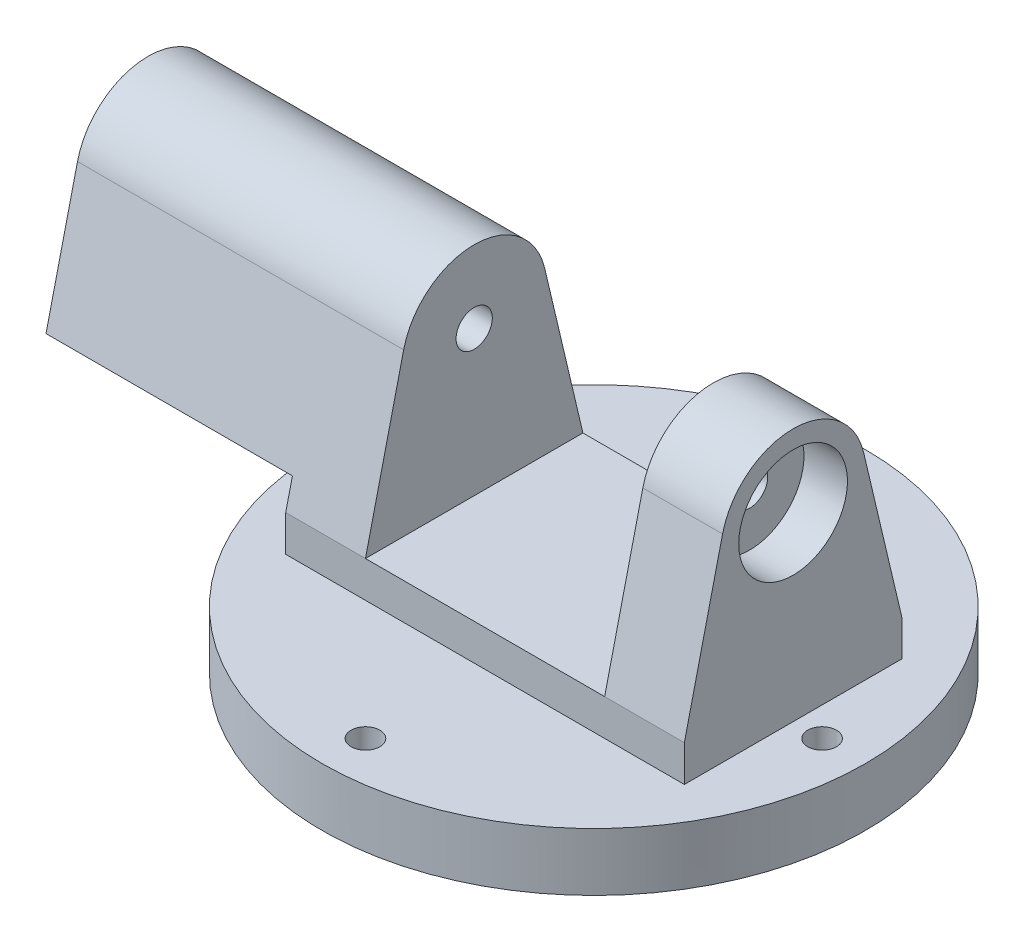
SolidWorks part; units mm, degrees
ref_plane "Alzado" through (0, 0, 0) normal (0, 0, 1) x (1, 0, 0)
ref_plane "Planta" through (0, 0, 0) normal (0, 1, 0) x (1, 0, 0)
ref_plane "Vista lateral" through (0, 0, 0) normal (1, 0, 0) x (0, 0, -1)
sketch "Croquis1" plane through (0, 0, 0) normal (0, 1, 0) x (1, 0, 0)
  circle A0 centre (0, 0) radius 75
extrude "Saliente-Extruir1" add sketch "Croquis1" along normal blind 8
sketch "Croquis2" plane through (0, 8, 0) normal (0, 1, 0) x (1, 0, 0)
  line L0 (0, 75) -> (0, 63) construction
  circle A0 centre (0, 0) radius 75 construction
  circle A1 centre (0, 63) radius 3.97
  circle A2 centre (63, 0) radius 3.97
  circle A3 centre (0, -63) radius 3.97
  circle A4 centre (-63, 0) radius 3.97
  point P15 (0, 0)
  dimension "D1" = 4
extrude "Cortar-Extruir1" cut sketch "Croquis2" against normal blind 20
sketch "Croquis3" plane through (0, 8, 0) normal (0, 1, 0) x (1, 0, 0)
  line L0 (-75, 0) -> (-55, 0) construction
  line L1 (75, 0) -> (55, 0) construction
  line L2 (-55, 0) -> (-55, 30)
  line L3 (-55, 30) -> (55, 30)
  line L4 (55, 30) -> (55, 0)
  line L5 (55, 0) -> (55, -30)
  line L6 (55, -30) -> (-55, -30)
  line L7 (-55, -30) -> (-55, 0)
  circle A0 centre (0, 0) radius 75 construction
extrude "Saliente-Extruir2" add sketch "Croquis3" along normal blind 10
sketch "Croquis4" plane through (55, 0, 0) normal (1, 0, 0) x (0, 0, -1)
  line L0 (-30, 18) -> (30, 18)
  line L2 (-30, 18) -> (-19.4643, 62.5982)
  line L3 (30, 18) -> (19.4643, 62.5982)
  arc A0 (19.4643, 62.5982) -> (-19.4643, 62.5982) centre (0, 58) ccw
extrude "Saliente-Extruir3" add sketch "Croquis4" against normal blind 22
mirror "Simetría1" about plane through (0, 0, 0) normal (1, 0, 0) of "Saliente-Extruir3"
sketch "Croquis5" plane through (-55, 0, 0) normal (-1, 0, 0) x (0, 0, 1)
  line L0 (0, 78) -> (0, 58) construction
  arc A0 (19.4643, 62.5982) -> (-19.4643, 62.5982) centre (0, 58) ccw construction
  circle A1 centre (0, 58) radius 15
extrude "Cortar-Extruir2" cut sketch "Croquis5" against normal blind 12
mirror "Simetría2" about plane through (0, 0, 0) normal (1, 0, 0) of "Cortar-Extruir2"
sketch "Croquis6" plane through (-43, 0, 0) normal (-1, 0, 0) x (0, 0, 1)
  line L0 (0, 73) -> (0, 58) construction
  circle A0 centre (0, 58) radius 15 construction
  circle A1 centre (0, 58) radius 5
extrude "Cortar-Extruir3" cut sketch "Croquis6" against normal blind 126
sketch "Croquis7" plane through (-55, 0, 0) normal (-1, 0, 0) x (0, 0, 1)
  line L0 (-19.4643, 62.5982) -> (-28.1515, 25.8247)
  line L1 (-30, 18) -> (-19.4643, 62.5982) construction
  line L2 (-28.1515, 25.8247) -> (28.1515, 25.8247)
  line L3 (19.4643, 62.5982) -> (30, 18) construction
  line L4 (28.1515, 25.8247) -> (19.4643, 62.5982)
  arc A0 (19.4643, 62.5982) -> (-19.4643, 62.5982) centre (0, 58) ccw
  circle A1 centre (0, 58) radius 15
extrude "Saliente-Extruir4" add sketch "Croquis7" along normal blind 68
sketch "Croquis8" plane through (0, 0, 0) normal (0, -1, 0) x (1, 0, 0)
  circle A2 centre (0, 0) radius 75
  circle A3 centre (0, 0) radius 75
  dimension "D1" = 0
extrude "Saliente-Extruir5" add sketch "Croquis8" along normal blind 8
sketch "Croquis9" plane through (0, -8, 0) normal (0, -1, 0) x (1, 0, 0)
  circle A0 centre (0, 0) radius 13
  circle A1 centre (0, 0) radius 15
  dimension "D1" = 26
  dimension "D2" = 30
extrude "Saliente-Extruir6" add sketch "Croquis9" along normal blind 18
sketch "Croquis10" plane through (43, 0, 0) normal (1, 0, 0) x (0, 0, -1)
  point P0 (0, 58)
